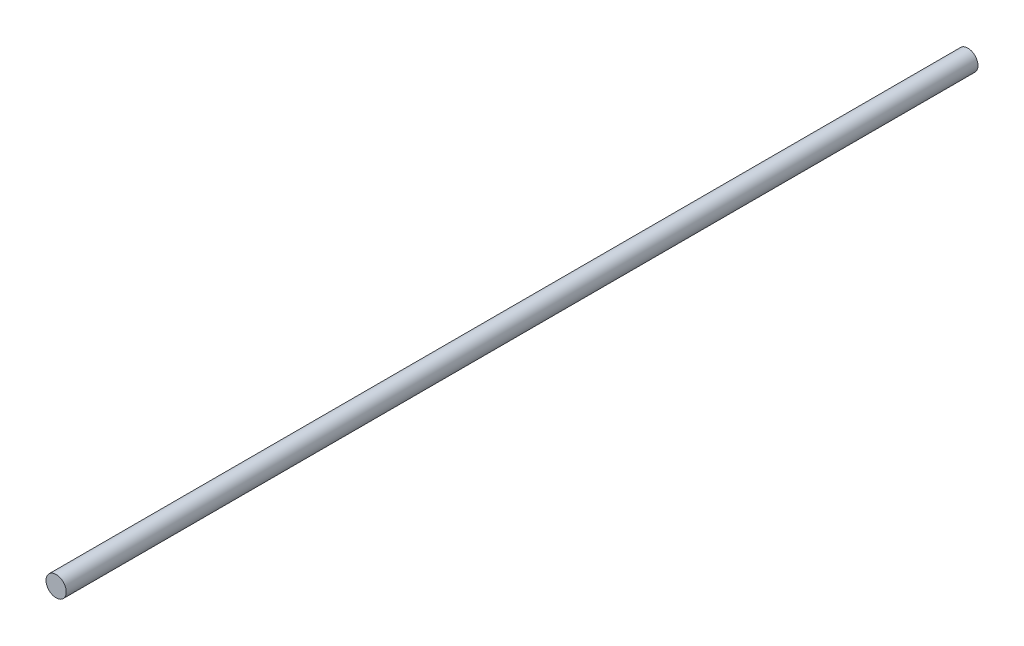
SolidWorks part; units mm, degrees
ref_plane "Front Plane" through (0, 0, 0) normal (0, 0, 1) x (1, 0, 0)
ref_plane "Top Plane" through (0, 0, 0) normal (0, 1, 0) x (1, 0, 0)
ref_plane "Right Plane" through (0, 0, 0) normal (1, 0, 0) x (0, 0, -1)
sketch "Sketch1" plane through (0, 0, 0) normal (0, 0, 1) x (1, 0, 0)
  circle A0 centre (0, 0) radius 3
  dimension "D1" = 6
extrude "Boss-Extrude1" add sketch "Sketch1" along normal blind 270
